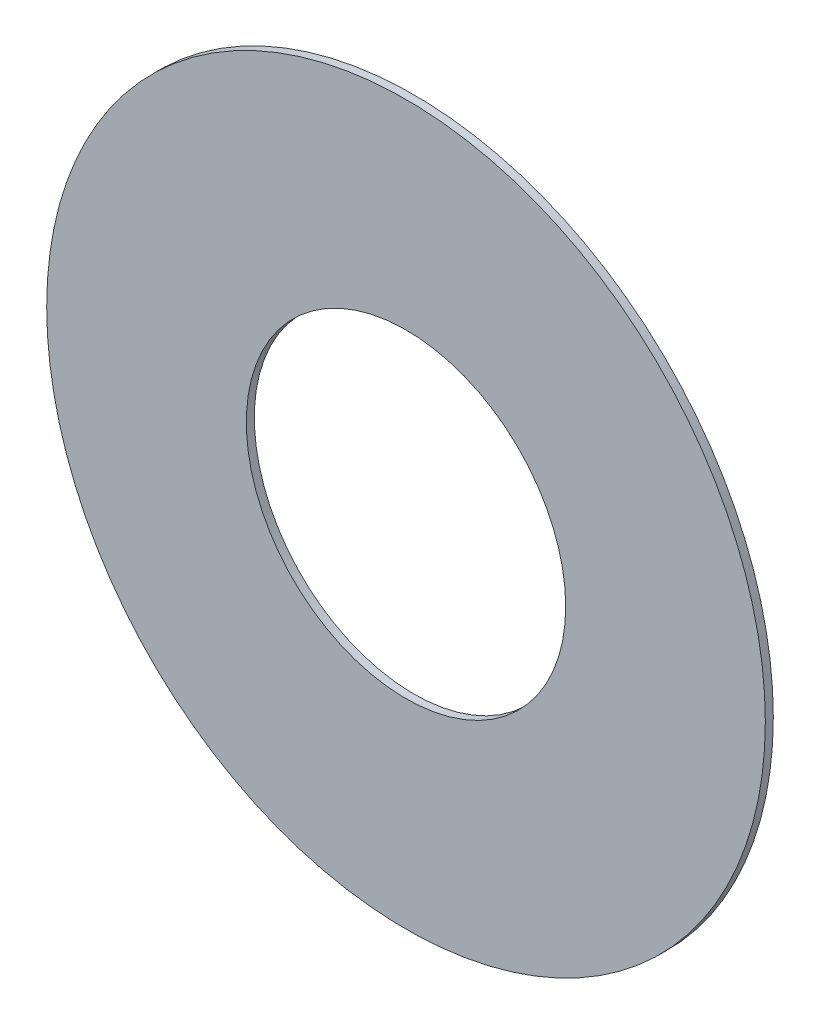
SolidWorks part; units mm, degrees
ref_plane "Plan1" through (0, 0, 0) normal (0, 0, 1) x (1, 0, 0)
ref_plane "Plan2" through (0, 0, 0) normal (0, 1, 0) x (1, 0, 0)
ref_plane "Plan3" through (0, 0, 0) normal (1, 0, 0) x (0, 0, -1)
sketch "Esquisse1" plane through (0, 0, 0) normal (0, 0, 1) x (1, 0, 0)
  circle A0 centre (0, 0) radius 4
  circle A1 centre (0, 0) radius 9
  dimension "D1" = 8
  dimension "D2" = 18
extrude "Base-Extrusion" add sketch "Esquisse1" along normal blind 0.2
